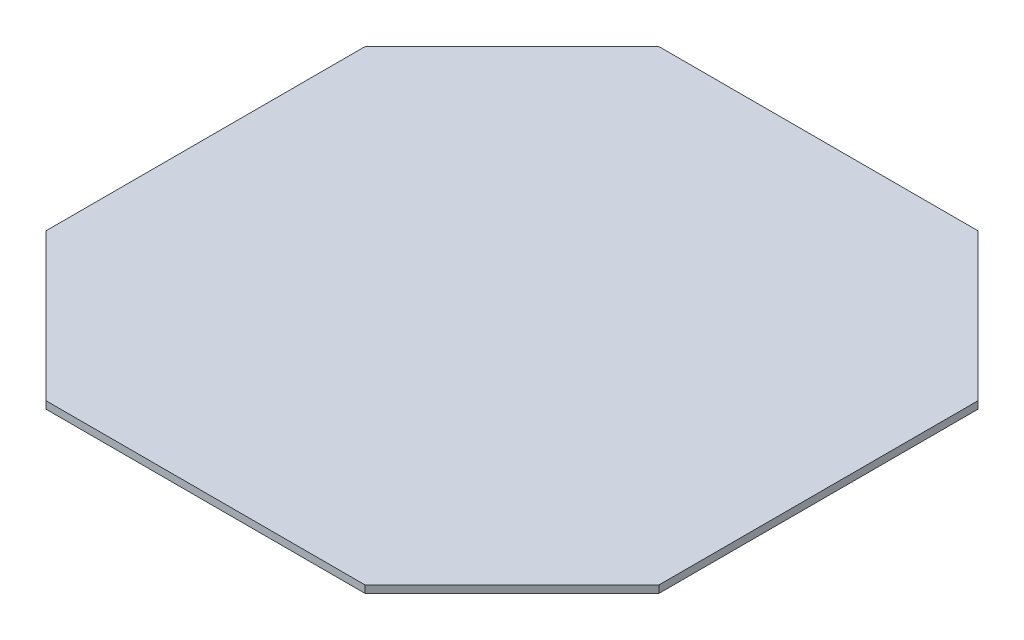
SolidWorks part; units mm, degrees
material "Alliage 1060"
ref_plane "Plan de face" through (0, 0, 0) normal (0, 0, 1) x (1, 0, 0)
ref_plane "Plan de dessus" through (0, 0, 0) normal (0, 1, 0) x (1, 0, 0)
ref_plane "Plan de droite" through (0, 0, 0) normal (1, 0, 0) x (0, 0, -1)
sketch "Esquisse1" plane through (0, 0, 0) normal (0, 1, 0) x (1, 0, 0)
  line L1 (125, -125) -> (-125, -125)
  line L2 (125, -125) -> (125, 125)
  line L3 (125, 125) -> (-125, 125)
  line L4 (-125, -125) -> (-125, 125)
  line L5 (125, -125) -> (-125, 125) construction
  line L6 (125, 125) -> (-125, -125) construction
  point P0 (0, 0)
  dimension "D1" = 250
  dimension "D2" = 250
extrude "Extrusion1" add sketch "Esquisse1" along normal blind 3
sketch "Esquisse2" plane through (0, 3, 0) normal (0, 1, 0) x (1, 0, 0)
  line L0 (125, 125) -> (-125, 125) construction
  line L1 (-125, 65) -> (-65, 125)
  line L2 (-125, 125) -> (-125, -125) construction
  line L3 (0, 0) -> (0, 158.815) construction
  line L4 (0, 158.815) -> (0, -168.7685) construction
  line L5 (0, 0) -> (167.1755, 0) construction
  line L6 (167.1755, 0) -> (-167.9322, 0) construction
  line L7 (65, 125) -> (125, 65)
  line L8 (-125, -65) -> (-65, -125)
  line L9 (-125, -125) -> (125, -125) construction
  line L10 (65, -125) -> (125, -65)
  line L11 (125, -125) -> (125, 125) construction
  line M1 (-125, 125) -> (-125, -125)
  line M2 (-125, -125) -> (125, -125)
  line M3 (125, -125) -> (125, 125)
  line M4 (125, 125) -> (-125, 125)
  dimension "D1" = 60
  dimension "D2" = 60
extrude "Extrusion11" cut sketch "Esquisse2" against normal blind 13 contours L1 M1 M4 | L7 M4 M3 | L10 M2 M3 | L8 M1 M2
